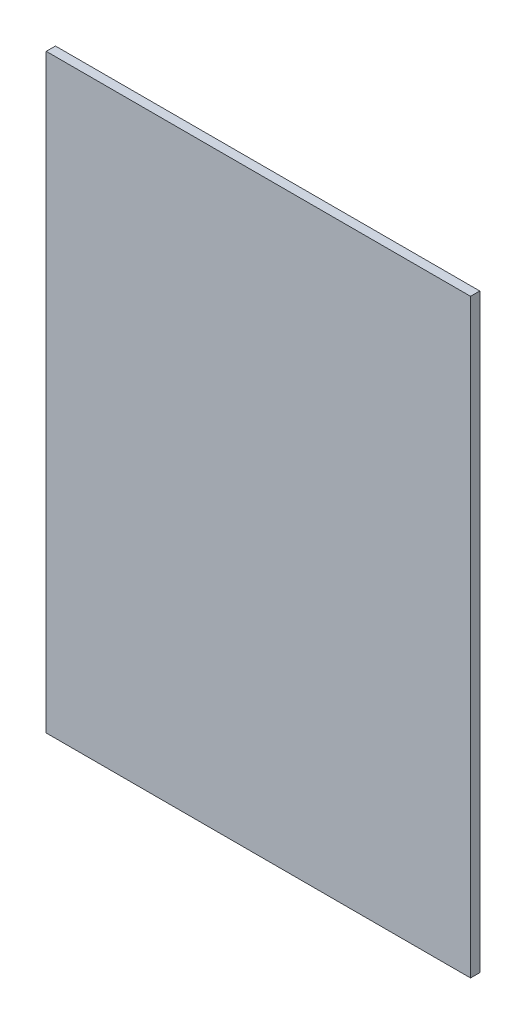
SolidWorks part; units mm, degrees
ref_plane "Front Plane" through (0, 0, 0) normal (0, 0, 1) x (1, 0, 0)
ref_plane "Top Plane" through (0, 0, 0) normal (0, 1, 0) x (1, 0, 0)
ref_plane "Right Plane" through (0, 0, 0) normal (1, 0, 0) x (0, 0, -1)
sketch "Sketch1" plane through (0, 0, 0) normal (0, 0, 1) x (1, 0, 0)
  line L1 (0, 0) -> (292.1, 0)
  line L2 (0, 0) -> (0, 406.4)
  line L3 (0, 406.4) -> (292.1, 406.4)
  line L4 (292.1, 0) -> (292.1, 406.4)
  dimension "D1" = 292.1
  dimension "D2" = 406.4
extrude "Boss-Extrude1" add sketch "Sketch1" along normal blind 6.35
